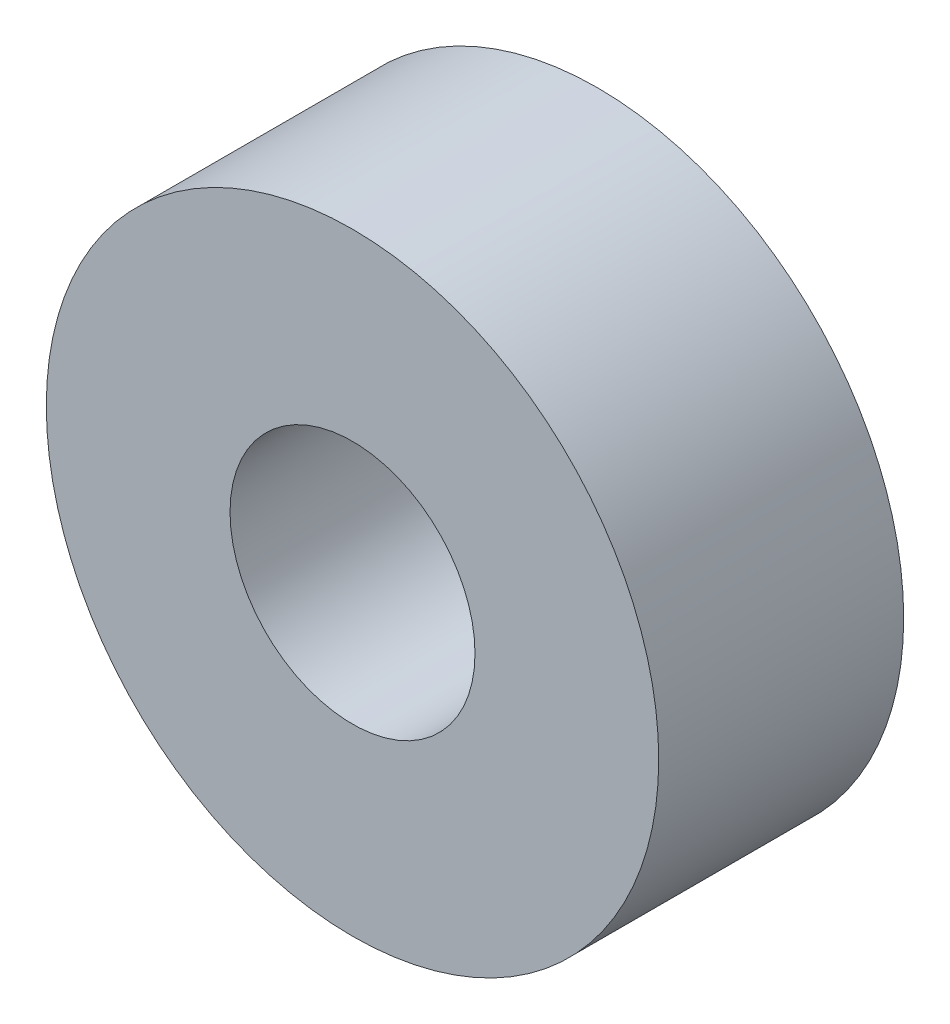
SolidWorks part; units mm, degrees
material "AISI 304"
ref_plane "前视基准面" through (0, 0, 0) normal (0, 0, 1) x (1, 0, 0)
ref_plane "上视基准面" through (0, 0, 0) normal (0, 1, 0) x (1, 0, 0)
ref_plane "右视基准面" through (0, 0, 0) normal (1, 0, 0) x (0, 0, -1)
sketch "草图1" plane through (0, 0, 0) normal (0, 0, 1) x (1, 0, 0)
  circle A0 centre (0, 0) radius 5
  circle A1 centre (0, 0) radius 2
  dimension "D1" = 4
  dimension "D2" = 10
extrude "凸台-拉伸1" add sketch "草图1" along normal blind 4
